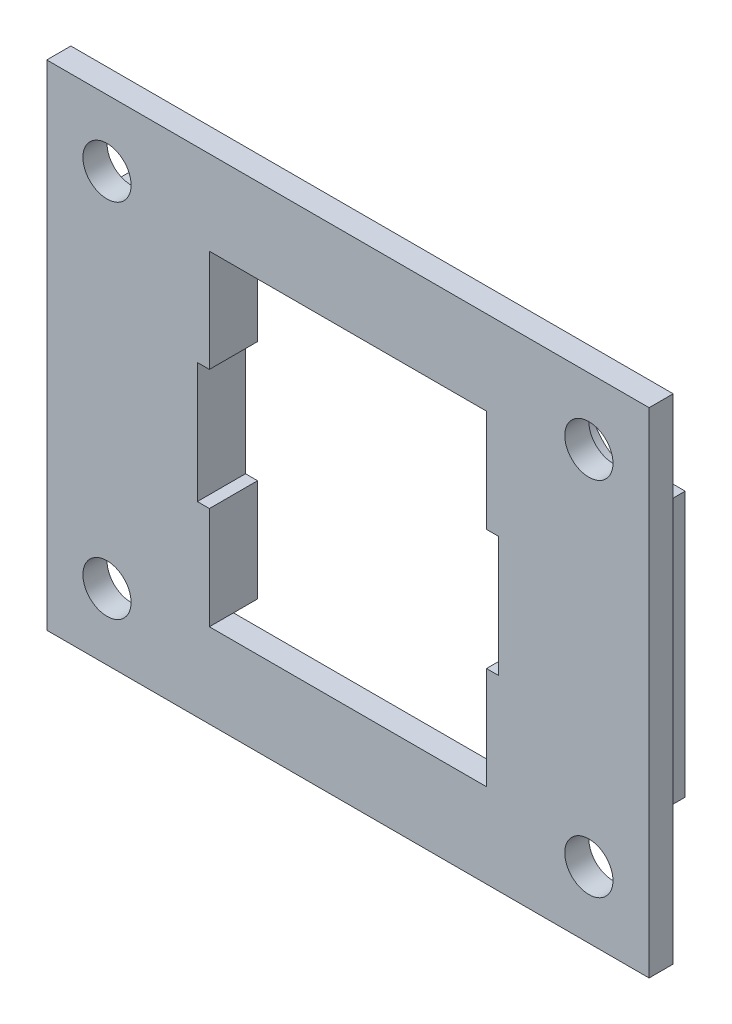
SolidWorks part; units mm, degrees
ref_plane "Front Plane" through (0, 0, 0) normal (0, 0, 1) x (1, 0, 0)
ref_plane "Top Plane" through (0, 0, 0) normal (0, 1, 0) x (1, 0, 0)
ref_plane "Right Plane" through (0, 0, 0) normal (1, 0, 0) x (0, 0, -1)
sketch "Sketch3" plane through (0, 0, 0) normal (0, 0, 1) x (1, 0, 0)
  line L0 (-10, 25) -> (40, 25)
  line L1 (0, 0) -> (30, 0)
  line L2 (0, 0) -> (0, 15)
  line L3 (0, 15) -> (30, 15)
  line L4 (30, 0) -> (30, 15)
  line L5 (40, -10) -> (40, 25)
  line L6 (-10, -10) -> (40, -10)
  line L7 (-10, -10) -> (-10, 25)
  dimension "D1" = 10
extrude "Boss-Extrude2" add sketch "Sketch3" along normal blind 8 contours L7 L0 L5 L6
sketch "Sketch1" plane through (0, 0, 0) normal (0, 0, 1) x (1, 0, 0)
  line L1 (0, 0) -> (30, 0) construction
  line L2 (0, 0) -> (0, 15) construction
  line L3 (0, 15) -> (30, 15) construction
  line L4 (30, 0) -> (30, 15) construction
  arc A0 (-0.3984, 17.2144) -> (0.3984, 17.2144) centre (0, 15) ccw
  arc A1 (-0.3984, 17.2144) -> (0.3984, 17.2144) centre (0, 17.25) ccw
  arc A2 (0.5367, 17.185) -> (1.2647, 16.8609) centre (0.9152, 17.0555) ccw
  arc A3 (0.5367, 17.185) -> (1.2647, 16.8609) centre (0, 15) ccw
  arc A4 (1.3791, 16.7778) -> (1.9122, 16.1857) centre (1.6721, 16.5055) ccw
  arc A5 (1.3791, 16.7778) -> (1.9122, 16.1857) centre (0, 15) ccw
  arc A6 (1.9829, 16.0632) -> (2.2292, 15.3054) centre (2.1399, 15.6953) ccw
  arc A7 (1.9829, 16.0632) -> (2.2292, 15.3054) centre (0, 15) ccw
  arc A8 (2.244, 15.1648) -> (2.1607, 14.3723) centre (2.2377, 14.7648) ccw
  arc A9 (2.244, 15.1648) -> (2.1607, 14.3723) centre (0, 15) ccw
  arc A10 (2.117, 14.2378) -> (1.7186, 13.5477) centre (1.9486, 13.875) ccw
  arc A11 (2.117, 14.2378) -> (1.7186, 13.5477) centre (0, 15) ccw
  arc A12 (1.6239, 13.4427) -> (0.9793, 12.9743) centre (1.3225, 13.1797) ccw
  arc A13 (1.6239, 13.4427) -> (0.9793, 12.9743) centre (0, 15) ccw
  arc A14 (0.8501, 12.9168) -> (0.0707, 12.7511) centre (0.4678, 12.7992) ccw
  arc A15 (0.8501, 12.9168) -> (0.0707, 12.7511) centre (0, 15) ccw
  arc A16 (-0.0707, 12.7511) -> (-0.8501, 12.9168) centre (-0.4678, 12.7992) ccw
  arc A17 (-0.0707, 12.7511) -> (-0.8501, 12.9168) centre (0, 15) ccw
  arc A18 (-0.9793, 12.9743) -> (-1.6239, 13.4427) centre (-1.3225, 13.1797) ccw
  arc A19 (-0.9793, 12.9743) -> (-1.6239, 13.4427) centre (0, 15) ccw
  arc A20 (-1.7186, 13.5477) -> (-2.117, 14.2378) centre (-1.9486, 13.875) ccw
  arc A21 (-1.7186, 13.5477) -> (-2.117, 14.2378) centre (0, 15) ccw
  arc A22 (-2.1607, 14.3723) -> (-2.244, 15.1648) centre (-2.2377, 14.7648) ccw
  arc A23 (-2.1607, 14.3723) -> (-2.244, 15.1648) centre (0, 15) ccw
  arc A24 (-2.2292, 15.3054) -> (-1.9829, 16.0632) centre (-2.1399, 15.6953) ccw
  arc A25 (-2.2292, 15.3054) -> (-1.9829, 16.0632) centre (0, 15) ccw
  arc A26 (-1.9122, 16.1857) -> (-1.3791, 16.7778) centre (-1.6721, 16.5055) ccw
  arc A27 (-1.9122, 16.1857) -> (-1.3791, 16.7778) centre (0, 15) ccw
  arc A28 (-1.2647, 16.8609) -> (-0.5367, 17.185) centre (-0.9152, 17.0555) ccw
  arc A29 (-1.2647, 16.8609) -> (-0.5367, 17.185) centre (0, 15) ccw
  point P52 (0, 15)
  dimension "D3" = 4.5
  dimension "D4" = 0.8
  dimension "D1" = 30
  dimension "D2" = 15
  dimension "D5" = 15
extrude "Cut-Extrude1" cut sketch "Sketch1" along normal blind 6 contours A28 A0 A26 A24 A22 A20 A18 A16 A14 A12 A10 A8 A6 A4 A2 A1
pattern_linear "LPattern1" count 2 spacing 15.5 along (0, -1, 0) count 2 spacing 30.51 along (1, 0, 0) of "Cut-Extrude1"
sketch "Sketch4" plane through (0, 0, 0) normal (0, 0, -1) x (-1, 0, 0)
  line L0 (-36, 21) -> (6, 21)
  line L1 (-40, -10) -> (10, -10)
  line L2 (-40, -10) -> (-40, 25)
  line L3 (-40, 25) -> (10, 25)
  line L4 (10, -10) -> (10, 25)
  line L5 (6, -6) -> (6, 21)
  line L6 (-36, -6) -> (6, -6)
  line L7 (-36, -6) -> (-36, 21)
  dimension "D1" = 4
extrude "Cut-Extrude2" cut sketch "Sketch4" against normal blind 6
sketch "Sketch5" plane through (0, 0, 0) normal (0, 0, -1) x (-1, 0, 0)
  line L0 (-27.5, 2.5) -> (-27.5, 12.5)
  line L1 (-36, -6) -> (6, -6)
  line L2 (-36, -6) -> (-36, 21)
  line L3 (-36, 21) -> (6, 21)
  line L4 (6, -6) -> (6, 21)
  line L5 (-27.5, 12.5) -> (-2.5, 12.5)
  line L6 (-2.5, 2.5) -> (-2.5, 12.5)
  line L7 (-27.5, 2.5) -> (-2.5, 2.5)
  dimension "D1" = 8.5
extrude "Cut-Extrude4" cut sketch "Sketch5" against normal blind 24 contours L5 L6 L7 L0
sketch "Sketch6" plane through (0, 0, 6) normal (0, 0, -1) x (-1, 0, 0)
  line L0 (-15, 12.5) -> (-2.5, 7.5) construction
  line L1 (-27.5, 12.5) -> (-2.5, 12.5) construction
  line L2 (-2.5, 2.5) -> (-2.5, 12.5) construction
  line L3 (-2.5, 7.5) -> (-15, 7.5) construction
  line L4 (-15, 7.5) -> (-15, 25.6664) construction
  line L5 (-15, 7.5) -> (-40, 7.5) construction
  line L6 (-40, 25) -> (-40, -10) construction
  line L7 (-40, 7.5) -> (10, 7.5) construction
  line L8 (10, -10) -> (10, 25) construction
  circle A0 centre (5, 22.5) radius 2
  dimension "D1" = 4
  dimension "D2" = 20
  dimension "D3" = 15
extrude "Cut-Extrude5" cut sketch "Sketch6" along normal blind 24 and the other way blind 24 contours A0
sketch "Sketch7" plane through (0, 0, 6) normal (0, 0, -1) x (-1, 0, 0)
  line L1 (10, 25) -> (-40, 25) construction
  line L2 (5, 25) -> (10, 25)
  line L3 (10, 25) -> (10, 20.5)
  line L4 (10, -10) -> (10, 25) construction
  line L6 (1.2919, 21) -> (1.2919, 25)
  line L7 (3.6771, 21) -> (-36, 21) construction
  line L8 (1.2919, 25) -> (5, 25)
  line L9 (5, 18.5) -> (10, 18.5)
  line L10 (10, 18.5) -> (10, 20.5)
  arc A0 (1.2919, 21) -> (5, 18.5) centre (5, 22.5) ccw
  dimension "D1" = 8
extrude "Cut-Extrude6" cut sketch "Sketch7" along normal blind 24
ref_plane "Plane1" through (15, 0, 0) normal (-1, 0, 0) x (0, 0, 1)
ref_plane "Plane2" through (0, 7.5, 0) normal (0, -1, 0) x (-1, 0, 0)
mirror "Mirror1" about plane through (15, 0, 0) normal (-1, 0, 0) of "Cut-Extrude5", "Cut-Extrude6"
mirror "Mirror2" about plane through (0, 7.5, 0) normal (0, -1, 0) of "Cut-Extrude5", "Cut-Extrude6", "Mirror1"
sketch "Sketch9" plane through (0, 0, 6) normal (0, 0, -1) x (-1, 0, 0)
  line L0 (10, -10) -> (10, 25) construction
  line L1 (-40, -13) -> (10, -13)
  line L2 (-40, -13) -> (-40, 28)
  line L3 (-40, 28) -> (10, 28)
  line L4 (10, -13) -> (10, 28)
  line L5 (10, 25) -> (-40, 25) construction
  line L6 (-40, -10) -> (10, -10) construction
  line L7 (-40, 25) -> (-40, -10) construction
  line L8 (-2.5, 2.5) -> (-2.5, 12.5) construction
  line L9 (-27.5, 12.5) -> (-2.5, 12.5) construction
  line L10 (-27.5, 2.5) -> (-27.5, 12.5) construction
  line L11 (-27.5, 2.5) -> (-2.5, 2.5) construction
  line L12 (-2.5, 2.5) -> (-2.5, 12.5)
  line L13 (-27.5, 12.5) -> (-2.5, 12.5)
  line L14 (-27.5, 2.5) -> (-27.5, 12.5)
  line L15 (-27.5, 2.5) -> (-2.5, 2.5)
  circle A0 centre (5, -7.5) radius 2 construction
  circle A1 centre (-35, -7.5) radius 2 construction
  circle A2 centre (5, 22.5) radius 2 construction
  circle A3 centre (-35, 22.5) radius 2 construction
  circle A4 centre (5, -7.5) radius 2
  circle A5 centre (-35, -7.5) radius 2
  circle A6 centre (5, 22.5) radius 2
  circle A7 centre (-35, 22.5) radius 2
  dimension "D1" = 3
  dimension "D2" = 3
extrude "Boss-Extrude4" add sketch "Sketch9" against normal up to surface (2 mm away) up to face at (37, -7.5, 8)
sketch "Sketch10" plane through (0, 0, 0) normal (0, 0, -1) x (-1, 0, 0)
  line L0 (-13.0739, 7.5) -> (-18.0697, 7.5) construction
  line L1 (-1.1, 7.5) -> (1.1, 7.5) construction
  line L2 (-18.0697, 7.5) -> (-15, 7.5) construction
  line L3 (-15, -4.4) -> (-15, 4.4) construction
  line L4 (-15, 7.5) -> (-15, 9.3565) construction
  line L6 (-36.5, -6.5) -> (6.5, -6.5)
  line L7 (-36.5, -6.5) -> (-36.5, 21.5)
  line L8 (-36.5, 21.5) -> (6.5, 21.5)
  line L9 (6.5, -6.5) -> (6.5, 21.5)
  line L10 (-36.5, -6.5) -> (6.5, 21.5) construction
  line L11 (-36.5, 21.5) -> (6.5, -6.5) construction
  dimension "D1" = 43
  dimension "D2" = 28
extrude "Cut-Extrude7" cut sketch "Sketch10" against normal blind 4 contours L7 L8 L9 L6
sketch "Sketch11" plane through (0, 0, 6) normal (0, 0, -1) x (-1, 0, 0)
  line L1 (6, -3.5) -> (8, -3.5)
  line L2 (6, -3.5) -> (6, 18.5)
  line L3 (6, 18.5) -> (8, 18.5)
  line L4 (8, -3.5) -> (8, 18.5)
  line L5 (-36, -3.5) -> (-38, -3.5)
  line L6 (-36, -3.5) -> (-36, 18.5)
  line L7 (-36, 18.5) -> (-38, 18.5)
  line L8 (-38, -3.5) -> (-38, 18.5)
  dimension "D1" = 2
  dimension "D2" = 2
extrude "Boss-Extrude5" add sketch "Sketch11" along normal blind 3
sketch "Sketch12" plane through (0, 0, 4) normal (0, 0, -1) x (-1, 0, 0)
  line L0 (-1.1, 7.5) -> (1.1, 7.5) construction
  line L1 (-3.5, -6) -> (-26.5, -6)
  line L2 (-3.5, -6) -> (-3.5, 21)
  line L3 (-3.5, 21) -> (-26.5, 21)
  line L4 (-26.5, -6) -> (-26.5, 21)
  line L5 (-3.5, -6) -> (-26.5, 21) construction
  line L6 (-3.5, 21) -> (-26.5, -6) construction
  line L7 (-15, -4.4) -> (-15, 4.4) construction
  line L8 (1.2919, -6) -> (-31.2919, -6) construction
  point P0 (-15, 7.5)
  dimension "D2" = 23
extrude "Cut-Extrude8" cut sketch "Sketch12" against normal blind 17
